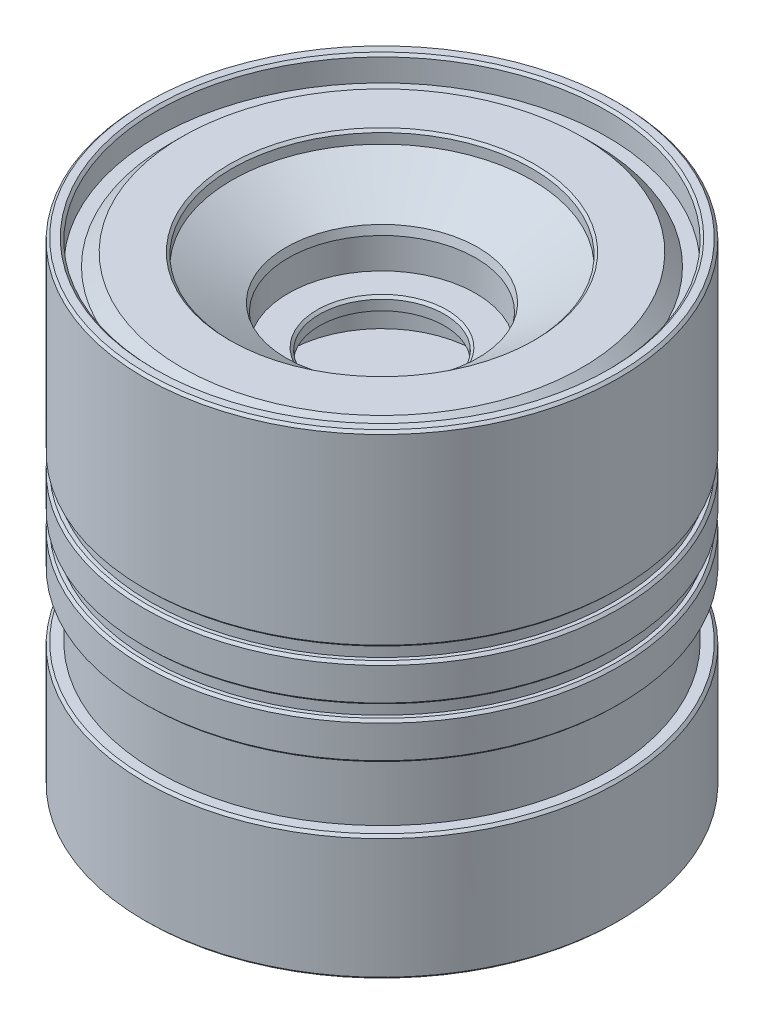
SolidWorks part; units mm, degrees
ref_plane "Front" through (0, 0, 0) normal (0, 0, 1) x (1, 0, 0)
ref_plane "Top" through (0, 0, 0) normal (0, 1, 0) x (1, 0, 0)
ref_plane "Right" through (0, 0, 0) normal (1, 0, 0) x (0, 0, -1)
sketch "Sketch2" plane through (0, 0, 0) normal (1, 0, 0) x (0, 0, -1)
  line L0 (-19, 0) -> (-19, 10)
  line L1 (-19, 10) -> (-18, 10)
  line L2 (-18, 10) -> (-18, 15)
  line L3 (-18, 15) -> (-19, 15)
  line L4 (-19, 15) -> (-19, 18)
  line L5 (-19, 18) -> (-18.5, 18)
  line L6 (-18.5, 18) -> (-18.5, 19)
  line L7 (-18.5, 19) -> (-19, 19)
  line L8 (-19, 19) -> (-19, 22)
  line L9 (-19, 22) -> (-18.5, 22)
  line L10 (-18.5, 22) -> (-18.5, 23)
  line L11 (-18.5, 23) -> (-19, 23)
  line L12 (-19, 23) -> (-19, 38)
  line L13 (-19, 38) -> (-18, 38)
  line L14 (-18, 38) -> (-18, 36)
  line L15 (-18, 36) -> (-17, 36)
  line L16 (-17, 36) -> (-16, 37)
  line L17 (0, 26.4019) -> (0, 0) construction
  line L18 (0, 0) -> (-19, 0)
  line L19 (-16, 37) -> (-12, 37)
  line L20 (-12, 37) -> (-12, 36)
  line L21 (-12, 36) -> (-7.5, 33.4019)
  line L22 (-7.5, 33.4019) -> (-7.5, 30.4019)
  line L23 (-7.5, 30.4019) -> (-5, 30.4019)
  line L24 (-5, 30.4019) -> (-5, 29.4019)
  line L25 (-5, 29.4019) -> (-7.5, 29.4019)
  line L26 (-7.5, 29.4019) -> (-7.5, 26.4019)
  line L27 (-7.5, 26.4019) -> (0, 26.4019)
  line L28 (0, 0) -> (0, 26.4019)
  dimension "D1" = 38
  dimension "D2" = 10
  dimension "D3" = 38
  dimension "D4" = 2
  dimension "D5" = 1
  dimension "D6" = 1
  dimension "D7" = 135
  dimension "D8" = 15
  dimension "D9" = 10
  dimension "D10" = 1
  dimension "D11" = 3
  dimension "D12" = 3
  dimension "D13" = 60
  dimension "D14" = 1
  dimension "D15" = 1
  dimension "D16" = 0.5
  dimension "D17" = 3
  dimension "D18" = 3
  dimension "D19" = 5
  dimension "D20" = 1
  dimension "D21" = 1
  dimension "D22" = 4
revolve "Revolve1" add sketch "Sketch2" angle 360 about L17
chamfer "Chamfer1" distance 0.2 angle 45 12 edges at (0, 38, 18) (0, 10, 19) (0, 0, 19) (0, 18, 19) (0, 15, 19) (0, 22, 19) (0, 19, 19) (0, 38, 19) (0, 23, 19) (0, 37, 12) (0, 30.4019, 5) (0, 33.4019, 7.5)
